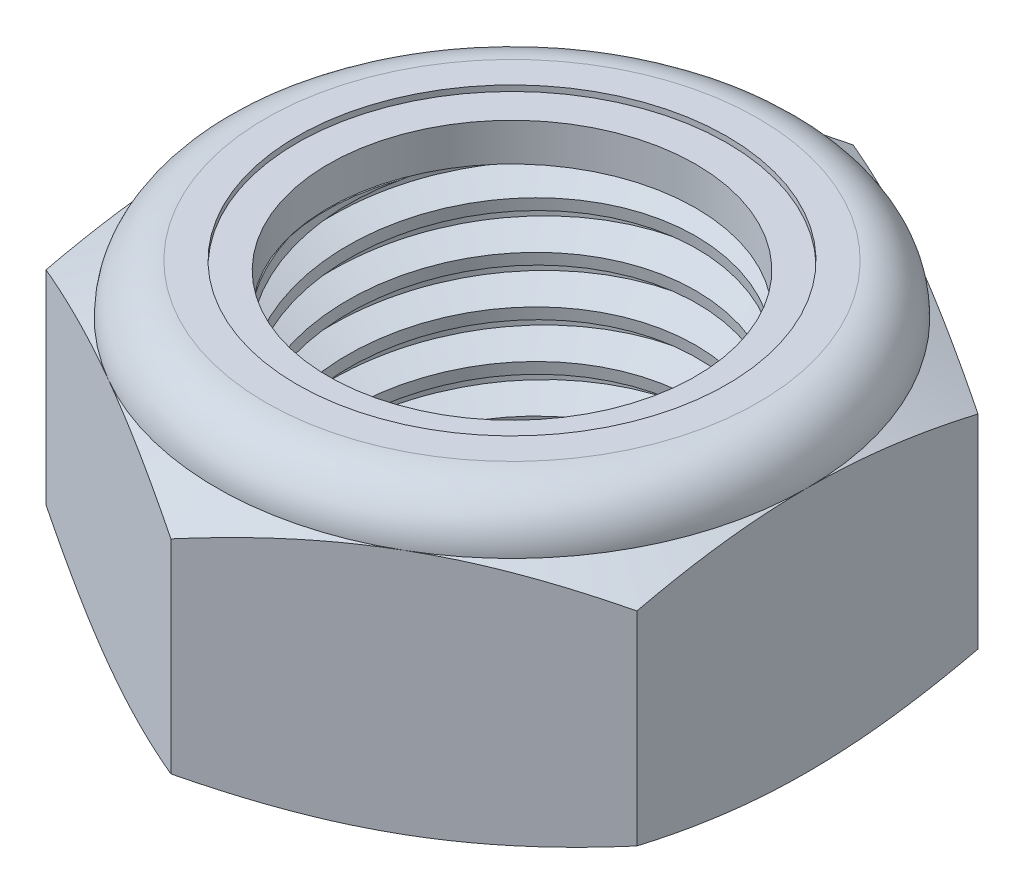
SolidWorks part; units mm, degrees
ref_plane "Front" through (0, 0, 0) normal (0, 0, 1) x (1, 0, 0)
ref_plane "Top" through (0, 0, 0) normal (0, 1, 0) x (1, 0, 0)
ref_plane "Right" through (0, 0, 0) normal (1, 0, 0) x (0, 0, -1)
sketch "Sketch1" plane through (0, 0, 0) normal (0, 1, 0) x (1, 0, 0)
  line L1 (0, 9.1654) -> (-7.9375, 4.5827)
  line L2 (-7.9375, 4.5827) -> (-7.9375, -4.5827)
  line L3 (-7.9375, -4.5827) -> (0, -9.1654)
  line L4 (0, -9.1654) -> (7.9375, -4.5827)
  line L5 (7.9375, -4.5827) -> (7.9375, 4.5827)
  line L6 (7.9375, 4.5827) -> (0, 9.1654)
  circle A0 centre (0, 0) radius 7.9375 construction
  dimension "Hex Flats" = 15.875
extrude "Extrude1" add sketch "Sketch1" along normal blind 7.9375
sketch "Sketch2" plane through (0, 0, 0) normal (1, 0, 0) x (0, 0, -1)
  line L0 (-5.5562, 0) -> (-5.5562, 7.9375) construction
  line L1 (0, 0) -> (5.5562, 0)
  line L2 (0, 0) -> (0, 7.9375)
  line L3 (0, 7.9375) -> (5.5562, 7.9375)
  line L4 (5.5562, 0) -> (5.5562, 7.9375)
  line L5 (-4.5827, 7.9375) -> (4.5827, 7.9375) construction
  line L7 (0, -5.5562) -> (0, 0) construction
  dimension "Thread Dia" = 11.1125
revolve "Revolve1" add sketch "Sketch2" angle 360 about L7
sketch "Sketch3" plane through (0, 0, 0) normal (1, 0, 0) x (0, 0, -1)
  line L0 (5.5562, 7.9375) -> (-5.5562, 7.9375) construction
  line L1 (-5.5562, 7.9375) -> (-5.5563, 6.6675) construction
  line L2 (-5.5563, 6.6675) -> (5.5562, 7.9375) construction
  line L3 (5.5562, 7.9375) -> (5.5743, 7.7798) construction
  line L4 (5.5743, 7.7798) -> (5.7005, 6.6757)
  line L5 (5.7005, 6.6757) -> (4.9724, 6.992)
  line L6 (4.9724, 6.992) -> (4.9364, 7.3074)
  line L7 (4.9364, 7.3074) -> (5.5743, 7.7798)
  line L8 (4.9544, 7.1497) -> (5.6374, 7.2277) construction
  line L9 (5.5562, 7.9375) -> (5.5562, 7.2185) construction
  line L10 (5.5562, 7.2185) -> (-5.5563, 5.9485) construction
  line L11 (-5.5563, 5.9485) -> (-5.5563, 6.6675) construction
  line L12 (-0.1547, 7.9375) -> (0.1547, 5.2294) construction
  line L13 (-5.5562, 0) -> (-5.5562, 7.9375) construction
  line L14 (0, 7.9375) -> (5.5562, 7.9375) construction
  line L15 (5.5562, 0) -> (5.5562, 7.9375) construction
  point P13 (0, 6.5835)
  dimension "D1" = 0.1588
  dimension "D2" = 0.3175
  dimension "Thread Pitch" = 1.27
  dimension "D4" = 60
  dimension "D5" = 1.27
revolve "Cut-Revolve1" cut sketch "Sketch3" angle 360 about L12
pattern_linear "LPattern1" count 6 spacing 1.27 along (0, -1, 0) count 2 spacing 1.27 along (0, 1, 0) of "Cut-Revolve1"
sketch "Sketch4" plane through (0, 0, 0) normal (1, 0, 0) x (0, 0, -1)
  line L0 (0, 7.9375) -> (5.5562, 7.9375)
  line L1 (5.5562, 7.9375) -> (4.9364, 7.6484)
  line L2 (4.9364, 7.6484) -> (4.9364, 0.2891)
  line L3 (4.9364, 0.2891) -> (5.5562, 0)
  line L4 (5.5562, 0) -> (0, 0)
  line L5 (0, 0) -> (0, 7.9375)
  line L6 (5.5562, 0) -> (5.5562, 7.9375) construction
  line L7 (0, 7.9375) -> (5.5562, 7.9375) construction
  line L8 (0, 0) -> (5.5562, 0) construction
  line L9 (0, 0) -> (0, 7.9375) construction
  line L10 (0, 7.9375) -> (0, 8.6215) construction
  dimension "D1" = 25
revolve "Cut-Revolve2" cut sketch "Sketch4" angle 360 about L10
combine bodies "Combine1" operation type subtract main body 112 bodies to subtract 111
sketch "Sketch5" plane through (0, 0, 0) normal (1, 0, 0) x (0, 0, -1)
  line L0 (0, 0) -> (7.9375, 0)
  line L1 (7.9375, 0) -> (9.1654, 0.5726)
  line L2 (9.1654, 0.5726) -> (9.1654, 6.042)
  line L3 (9.1654, 6.042) -> (7.9375, 6.6146)
  line L4 (6.6146, 7.9375) -> (6.6146, 9.2075)
  line L5 (6.6146, 9.2075) -> (10.4354, 9.2075)
  line L6 (10.4354, 9.2075) -> (10.4354, -1.27)
  line L7 (10.4354, -1.27) -> (0, -1.27)
  line L8 (0, -1.27) -> (0, 0)
  line L9 (7.9375, 6.6146) -> (7.9375, 0) construction
  line L10 (0, 0) -> (5.5562, 0) construction
  line L13 (9.1654, 3.3073) -> (10.4354, 3.3073) construction
  line L14 (9.1654, 7.9375) -> (9.1654, 0) construction
  line L15 (0, 0) -> (0, 9.2075) construction
  line L20 (0, 9.2075) -> (6.6146, 9.2075) construction
  line L22 (0, 7.9375) -> (5.5562, 7.9375) construction
  arc A0 (7.9375, 6.6146) -> (6.6146, 7.9375) centre (6.6146, 6.6146) ccw
  dimension "D1" = 25
  dimension "D2" = 1.27
  dimension "D3" = 7.9375
  dimension "D4" = 1.3229
revolve "Cut-Revolve3" cut sketch "Sketch5" angle 360 about L15
sketch "Sketch6" plane through (0, 0, 0) normal (1, 0, 0) x (0, 0, -1)
  line L0 (0, 6.6146) -> (7.7851, 6.6146)
  line L1 (6.6146, 7.7851) -> (5.7755, 7.7851)
  line L2 (0, 9.2075) -> (0, 6.6146)
  line L3 (5.7755, 9.2075) -> (0, 9.2075)
  line L4 (0, 9.2075) -> (6.6146, 9.2075) construction
  line L5 (0, 0) -> (0, 9.2075) construction
  line L6 (0, 9.2075) -> (0, 44.323) construction
  line L7 (5.7755, 7.7851) -> (5.7755, 9.2075)
  line L8 (6.6146, 7.9375) -> (6.6146, 7.7851) construction
  line L9 (5.7755, 7.7851) -> (4.9364, 7.7851) construction
  line L10 (4.9364, 7.7851) -> (4.9364, 7.6484) construction
  arc A0 (7.7851, 6.6146) -> (6.6146, 7.7851) centre (6.6146, 6.6146) ccw
  arc A1 (7.9375, 6.6146) -> (6.6146, 7.9375) centre (6.6146, 6.6146) ccw construction
  dimension "D1" = 0.1524
revolve "Cut-Revolve4" cut sketch "Sketch6" angle 360 about L6
sketch "Sketch7" plane through (0, 0, 0) normal (1, 0, 0) x (0, 0, -1)
  line L0 (4.9364, 6.6908) -> (7.7062, 6.6908)
  line L1 (6.6146, 7.7089) -> (4.9364, 7.7089)
  line L2 (4.9364, 7.7089) -> (4.9364, 6.6908)
  line L3 (4.9364, 6.6908) -> (0, 6.6908) construction
  line L4 (0, 6.6908) -> (0, 7.7089) construction
  line L5 (0, 7.7089) -> (4.9364, 7.7089) construction
  line L6 (4.9364, 6.6908) -> (4.9364, 6.6146) construction
  line L7 (0, 6.6146) -> (7.7851, 6.6146) construction
  line L8 (6.6146, 7.7089) -> (6.6146, 7.7851) construction
  arc A0 (7.7062, 6.6908) -> (6.6146, 7.7089) centre (6.6146, 6.6146) ccw
  arc A2 (7.7851, 6.6146) -> (6.6146, 7.7851) centre (6.6146, 6.6146) ccw construction
  dimension "D1" = 0.0762
revolve "Revolve2" add sketch "Sketch7" angle 360 about L4
equation "\"D1@Sketch3\"=\"Thread Pitch@Sketch3\"/8"
equation "\"D2@Sketch3\"=\"Thread Pitch@Sketch3\"/4"
equation "\"D5@Sketch3\"=\"Thread Pitch@Sketch3\""
equation "\"D4@LPattern1\"=\"Thread Pitch@Sketch3\""
equation "\"D3@LPattern1\"=\"Thread Pitch@Sketch3\""
equation "\"D1@LPattern1\"=\"Height@Extrude1\"/\"Thread Pitch@Sketch3\""
equation "\"D4@Sketch5\"=\"Height@Extrude1\"/6"
